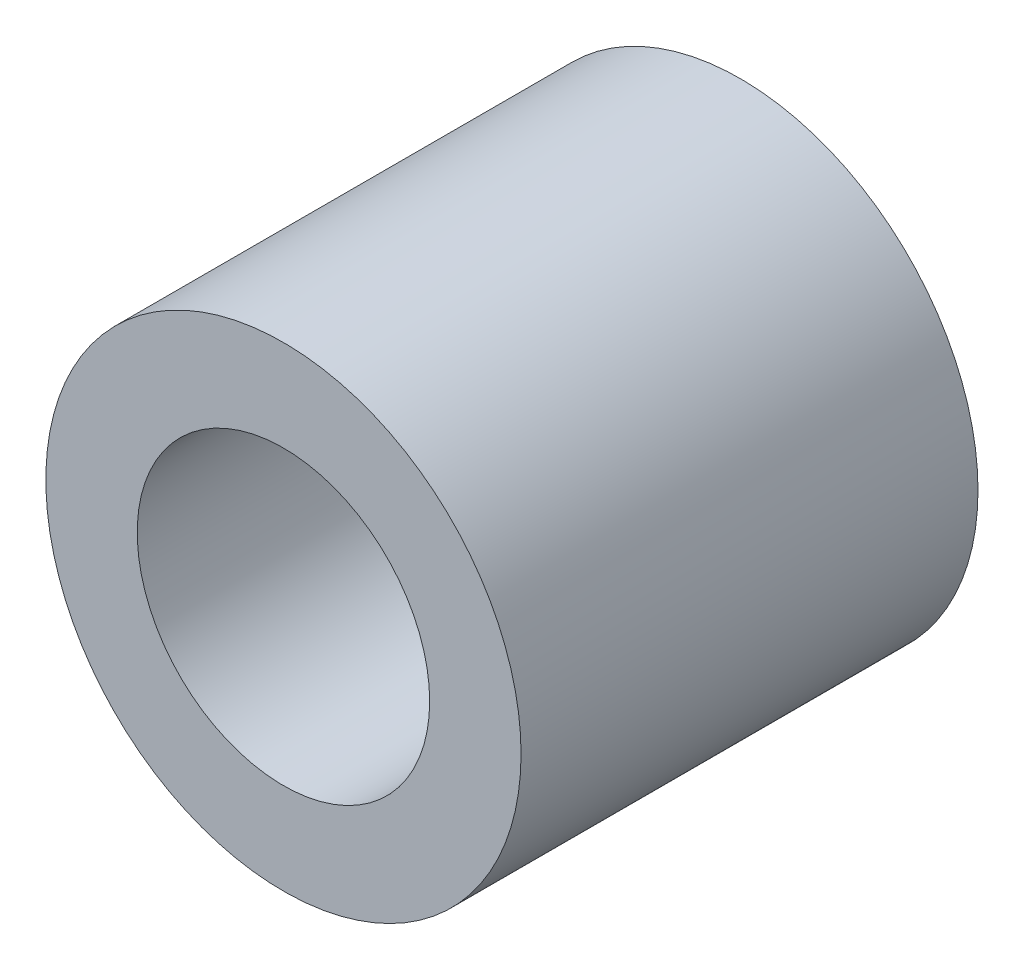
SolidWorks part; units mm, degrees
ref_plane "Front Plane" through (0, 0, 0) normal (0, 0, 1) x (1, 0, 0)
ref_plane "Top Plane" through (0, 0, 0) normal (0, 1, 0) x (1, 0, 0)
ref_plane "Right Plane" through (0, 0, 0) normal (1, 0, 0) x (0, 0, -1)
sketch "Sketch1" plane through (0, 0, 0) normal (0, 0, 1) x (1, 0, 0)
  circle A0 centre (1.45, 331) radius 2.6
extrude "Boss-Extrude1" add sketch "Sketch1" along normal blind 5
hole_wizard "M3 Clearance Hole1" positions "Sketch3" profile "Sketch2" hole size "M3" standard "ANSI Metric"
sketch "Sketch3" plane through (0, 0, 5) normal (0, 0, 1) x (1, 0, 0)
  point P0 (1.45, 331)
sketch "Sketch2" plane through (1.45, 331, 5) normal (1, 0, 0) x (0, -1, 0)
  line L0 (0, 0) -> (0, 7.9614)
  line L1 (0, 7.9614) -> (1.6, 7)
  line L2 (1.6, 7) -> (1.6, 0)
  line L5 (1.6, 0) -> (0, 0)
  line L10 (0, 7.9614) -> (-1.6, 7) construction
  line L11 (0, -6.35) -> (0, 107.95) construction
  dimension "Hole Dia." = 3.2
  dimension "Hole Depth" = 7
  dimension "Drill Angle" = 118
